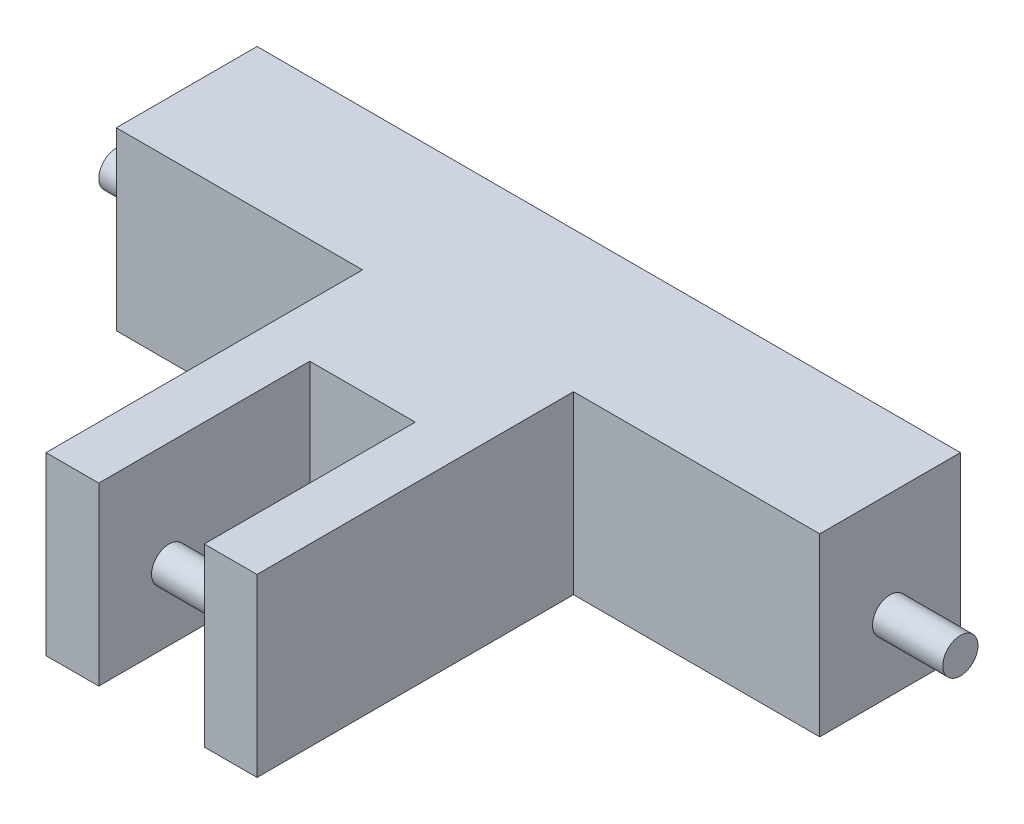
SolidWorks part; units mm, degrees
ref_plane "Front Plane" through (0, 0, 0) normal (0, 0, 1) x (1, 0, 0)
ref_plane "Top Plane" through (0, 0, 0) normal (0, 1, 0) x (1, 0, 0)
ref_plane "Right Plane" through (0, 0, 0) normal (1, 0, 0) x (0, 0, -1)
sketch "Sketch1" plane through (0, 0, 0) normal (0, 1, 0) x (1, 0, 0)
  line L0 (-50, 20) -> (50, 20)
  line L1 (50, 20) -> (50, 0)
  line L2 (50, 0) -> (15, 0)
  line L3 (15, 0) -> (15, -45)
  line L4 (15, -45) -> (-15, -45)
  line L5 (-15, -45) -> (-15, 0)
  line L6 (-15, 0) -> (-50, 0)
  line L7 (-50, 0) -> (-50, 20)
  line L8 (0, -45) -> (0, 20) construction
  point P12 (16.4197, -24.9562)
  dimension "D1" = 100
  dimension "D2" = 30
  dimension "D3" = 45
  dimension "D4" = 20
extrude "Boss-Extrude1" add sketch "Sketch1" along normal blind 25
sketch "Sketch2" plane through (0, 0, 45) normal (0, 0, 1) x (1, 0, 0)
  line L0 (-15, 0) -> (15, 0) construction
  line L1 (-7.5, 0) -> (7.5, 0)
  line L2 (-7.5, 0) -> (-7.5, 30)
  line L3 (-7.5, 30) -> (7.5, 30)
  line L4 (7.5, 0) -> (7.5, 30)
  line L5 (0, 30) -> (0, 0) construction
  point P8 (0, 0)
  point P9 (6.7999, 20)
  dimension "D1" = 15
  dimension "D2" = 30
extrude "Cut-Extrude1" cut sketch "Sketch2" against normal blind 30
sketch "Sketch3" plane through (50, 0, 0) normal (1, 0, 0) x (0, 0, -1)
  circle A0 centre (10, 10) radius 2.5
  dimension "D3" = 5
  dimension "D1" = 10
  dimension "D2" = 10
extrude "Boss-Extrude2" add sketch "Sketch3" along normal blind 10
mirror "Mirror1" about plane through (0, 0, 0) normal (1, 0, 0) of "Boss-Extrude2"
sketch "Sketch5" plane through (-7.5, 0, 0) normal (1, 0, 0) x (0, 0, -1)
  circle A0 centre (-35, 10) radius 2.5
  dimension "D1" = 5
  dimension "D2" = 10
  dimension "D3" = 35
extrude "Boss-Extrude3" add sketch "Sketch5" along normal up to next
